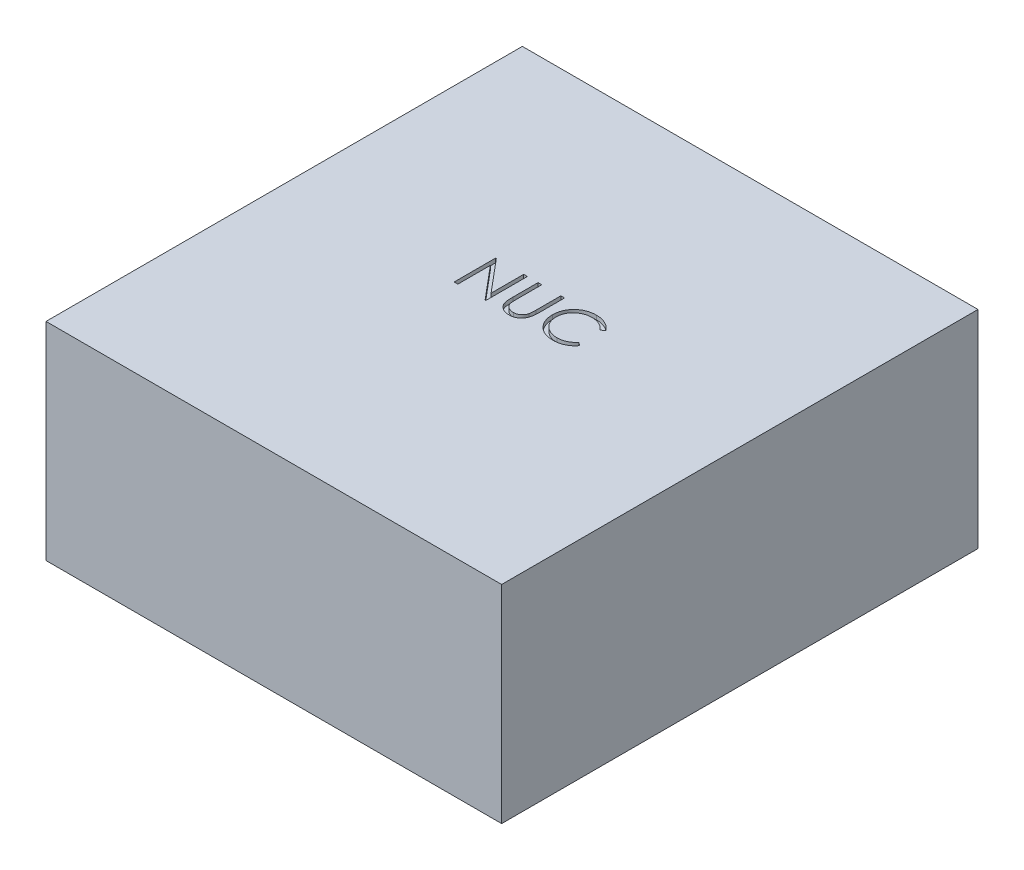
SolidWorks part; units mm, degrees
ref_plane "Front Plane" through (0, 0, 0) normal (0, 0, 1) x (1, 0, 0)
ref_plane "Top Plane" through (0, 0, 0) normal (0, 1, 0) x (1, 0, 0)
ref_plane "Right Plane" through (0, 0, 0) normal (1, 0, 0) x (0, 0, -1)
sketch "Sketch1" plane through (0, 0, 0) normal (0, 1, 0) x (1, 0, 0)
  line L1 (0, 0) -> (110, 0)
  line L2 (0, 0) -> (0, 115)
  line L3 (0, 115) -> (110, 115)
  line L4 (110, 0) -> (110, 115)
  dimension "D1" = 115
  dimension "D2" = 110
extrude "Boss-Extrude1" add sketch "Sketch1" along normal blind 50
sketch "Sketch2" plane through (0, 50, 0) normal (0, 1, 0) x (1, 0, 0)
  line L0 (0, 57.5) -> (110, 57.5) construction
  line L1 (0, 115) -> (0, 0) construction
  line L2 (110, 0) -> (110, 115) construction
  text T0 "NUC" font "Century Gothic" height 10
extrude "Cut-Extrude1" cut sketch "Sketch2" against normal blind 1
